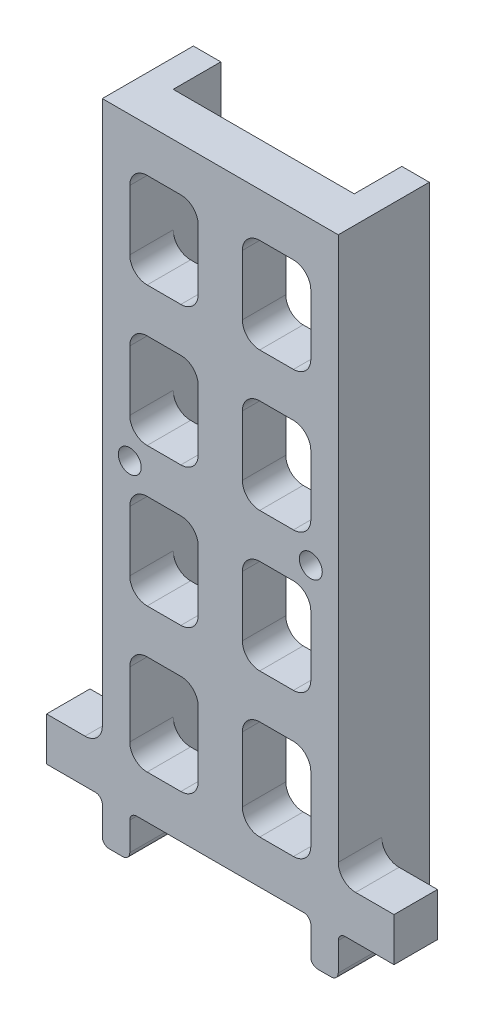
SolidWorks part; units mm, degrees
material "ABS PC"
ref_plane "Front Plane" through (0, 0, 0) normal (0, 0, 1) x (1, 0, 0)
ref_plane "Top Plane" through (0, 0, 0) normal (0, 1, 0) x (1, 0, 0)
ref_plane "Right Plane" through (0, 0, 0) normal (1, 0, 0) x (0, 0, -1)
sketch "Sketch1" plane through (0, 0, 0) normal (0, 1, 0) x (1, 0, 0)
  line L1 (-1.975, 0) -> (1.975, 0)
  line L2 (-1.975, 0) -> (-1.975, 13.1)
  line L3 (-1.975, 13.1) -> (1.975, 13.1)
  line L4 (1.975, 0) -> (1.975, 13.1)
  point P4 (0, 0)
  dimension "D1" = 3.95
  dimension "D2" = 13.1
extrude "Boss-Extrude1" add sketch "Sketch1" along normal blind 93
sketch "Sketch2" plane through (0, 0, 0) normal (0, 1, 0) x (1, 0, 0)
  line L0 (-1.975, 13.1) -> (-1.975, 0) construction
  line L1 (28.025, 13.1) -> (31.975, 13.1)
  line L2 (28.025, 13.1) -> (28.025, 0)
  line L3 (28.025, 0) -> (31.975, 0)
  line L4 (-1.975, 13.1) -> (-1.975, 0)
  line L5 (-1.975, 0) -> (1.975, 0)
  line L6 (1.975, 0) -> (1.975, 13.1)
  line L7 (1.975, 13.1) -> (-1.975, 13.1)
  line L8 (-1.975, 13.1) -> (-1.975, 0) construction
  line L9 (-1.975, 0) -> (1.975, 0) construction
  line L10 (1.975, 0) -> (1.975, 13.1) construction
  line L11 (1.975, 13.1) -> (-1.975, 13.1) construction
  line L12 (31.975, 13.1) -> (31.975, 0)
  point P11 (30, 0)
  dimension "D2" = 30
  dimension "D1" = 0
extrude "Boss-Extrude2" add sketch "Sketch2" along normal up to surface (93 mm away) separate body up to face at (0, 93, -6.55)
sketch "Sketch3" plane through (1.975, 0, 0) normal (1, 0, 0) x (0, 0, -1)
  line L0 (0, 93) -> (0, 0) construction
  line L1 (0, 93) -> (6.25, 93)
  line L2 (0, 93) -> (0, 86.65)
  line L3 (0, 86.65) -> (6.25, 86.65)
  line L4 (6.25, 93) -> (6.25, 86.65)
  line L5 (13.1, 93) -> (13.1, 0) construction
  line L6 (0, 93) -> (13.1, 93) construction
  dimension "D1" = 6.85
  dimension "D2" = 6.35
  dimension "D3" = 0
extrude "Boss-Extrude3" add sketch "Sketch3" along normal up to next (30 mm away)
pattern_linear "LPattern1" count 4 spacing 20 along (0, -1, 0) of "Boss-Extrude3"
sketch "Sketch4" plane through (0, 86.65, 0) normal (0, -1, 0) x (1, 0, 0)
  line L0 (28.025, 0) -> (1.975, 0) construction
  line L1 (11.825, 0) -> (18.175, 0)
  line L2 (11.825, 0) -> (11.825, -6.25)
  line L3 (11.825, -6.25) -> (18.175, -6.25)
  line L4 (18.175, 0) -> (18.175, -6.25)
  line L5 (28.025, -6.25) -> (1.975, -6.25) construction
  point P8 (15, 0)
  point P9 (15, 0)
  dimension "D1" = 6.35
extrude "Boss-Extrude4" add sketch "Sketch4" along normal up to surface (60 mm away) up to face at (15, 26.65, -3.125)
fillet "Fillet1" radius 2.5 24 edges at (18.175, 33, -3.125) (28.025, 33, -3.125) (28.025, 46.65, -3.125) (18.175, 46.65, -3.125) (1.975, 46.65, -3.125) (11.825, 46.65, -3.125) (11.825, 33, -3.125) (1.975, 33, -3.125) (1.975, 73, -3.125) (11.825, 73, -3.125) (11.825, 86.65, -3.125) (1.975, 86.65, -3.125) (1.975, 66.65, -3.125) (11.825, 66.65, -3.125) (11.825, 53, -3.125) (1.975, 53, -3.125) (18.175, 53, -3.125) (28.025, 53, -3.125) (28.025, 66.65, -3.125) (18.175, 66.65, -3.125) (28.025, 73, -3.125) (18.175, 73, -3.125) (18.175, 86.65, -3.125) (28.025, 86.65, -3.125)
ref_plane "Plane1" through (15, 0, 0) normal (-1, 0, 0) x (0, 0, 1)
sketch "Sketch5" plane through (15, 0, 0) normal (-1, 0, 0) x (0, 0, 1)
  line L0 (0, 93) -> (0, 0) construction
  line L1 (0, 12.3) -> (-6.25, 12.3)
  line L2 (0, 12.3) -> (0, 6.05)
  line L3 (0, 6.05) -> (-6.25, 6.05)
  line L4 (-6.25, 12.3) -> (-6.25, 6.05)
  line L5 (-13.1, 0) -> (0, 0) construction
  dimension "D1" = 6.25
  dimension "D2" = 6.05
extrude "Boss-Extrude5" add sketch "Sketch5" along normal mid plane 50
fillet "Fillet2" radius 2.5 4 edges at (28.025, 12.3, -3.125) (1.975, 12.3, -3.125) (1.975, 26.65, -3.125) (28.025, 26.65, -3.125)
fillet "Fillet3" radius 2.5 2 edges at (31.975, 12.3, -3.125) (-1.975, 12.3, -3.125)
sketch "Sketch6" plane through (0, 26.65, 0) normal (0, -1, 0) x (1, 0, 0)
  line L0 (25.525, 0) -> (4.475, 0) construction
  line L1 (18.175, 0) -> (11.825, 0)
  line L2 (18.175, 0) -> (18.175, -6.25)
  line L3 (18.175, -6.25) -> (11.825, -6.25)
  line L4 (11.825, 0) -> (11.825, -6.25)
  line L5 (25.525, -6.25) -> (4.475, -6.25) construction
  line L6 (11.825, 0) -> (11.825, -6.25) construction
  point P8 (15, 0)
  point P10 (15, 0)
extrude "Boss-Extrude6" add sketch "Sketch6" along normal up to surface (14.35 mm away) up to face at (15, 12.3, -3.125)
fillet "Fillet4" radius 2.5 4 edges at (11.825, 12.3, -3.125) (18.175, 12.3, -3.125) (18.175, 26.65, -3.125) (11.825, 26.65, -3.125)
sketch "Sketch7" plane through (0, 0, 0) normal (0, 0, 1) x (1, 0, 0)
  line L0 (-1.975, 93) -> (-1.975, 0) construction
  line L1 (31.975, 93) -> (-1.975, 93)
  line L2 (31.975, 93) -> (31.975, 79.825)
  line L3 (31.975, 79.825) -> (-1.975, 79.825)
  line L4 (-1.975, 93) -> (-1.975, 79.825)
extrude "Cut-Extrude2" [suppressed] cut sketch "Sketch7" against normal through all flip side to cut
sketch "Sketch8" plane through (0, 0, 0) normal (0, 0, 1) x (1, 0, 0)
  line L0 (23.1, 53) -> (23.1, 46.65) construction
  line L1 (25.525, 53) -> (20.675, 53) construction
  line L2 (25.525, 46.65) -> (20.675, 46.65) construction
  line L3 (-1.975, 49.825) -> (31.975, 49.825) construction
  line L4 (-1.975, 93) -> (-1.975, 14.8) construction
  line L5 (31.975, 93) -> (31.975, 14.8) construction
  line L6 (6.9, 53) -> (6.9, 46.65) construction
  line L7 (9.325, 53) -> (4.475, 53) construction
  line L8 (9.325, 46.65) -> (4.475, 46.65) construction
  line L9 (15, 93) -> (15, 6.05) construction
  line L10 (-1.975, 93) -> (31.975, 93) construction
  line L11 (1.975, 6.05) -> (28.025, 6.05) construction
  line L12 (1.975, 59.825) -> (1.975, 39.825) construction
  line L13 (1.975, 64.15) -> (1.975, 55.5) construction
  line L14 (1.975, 44.15) -> (1.975, 35.5) construction
  line L15 (28.025, 59.825) -> (28.025, 39.825) construction
  line L16 (28.025, 64.15) -> (28.025, 55.5) construction
  line L17 (28.025, 44.15) -> (28.025, 35.5) construction
  line L18 (1.975, 59.825) -> (-1.975, 59.825) construction
  line L19 (0, 59.825) -> (0, 49.825) construction
  point P41 (30, 49.825)
  point P43 (0, 49.825)
  point P44 (6.9, 49.825)
  point P48 (23.1, 49.825)
  point P51 (1.975, 49.825)
  point P53 (28.025, 49.825)
hole_wizard "Ø3.3 (3.3) Diameter Hole1" positions "Sketch8" profile "Sketch9" hole size "Ø3.3" standard "ANSI Metric"
sketch "Sketch9" plane through (28.025, 49.825, 0) normal (1, 0, 0) x (0, -1, 0)
  line L0 (0, 0) -> (0, 5.9914)
  line L1 (0, 5.9914) -> (1.65, 5)
  line L2 (1.65, 5) -> (1.65, 0)
  line L5 (1.65, 0) -> (0, 0)
  line L10 (0, 5.9914) -> (-1.65, 5) construction
  line L11 (0, -6.35) -> (0, 107.95) construction
  dimension "Hole Dia." = 3.3
  dimension "Hole Depth" = 5
  dimension "Drill Angle" = 118
fillet "Fillet5" radius 1 4 edges at (31.975, 0, -6.55) (28.025, 0, -6.55) (1.975, 0, -6.55) (-1.975, 0, -6.55)
fillet "Fillet6" radius 1 4 edges at (1.975, 6.05, -3.125) (-1.975, 6.05, -3.125) (31.975, 6.05, -3.125) (28.025, 6.05, -3.125)
